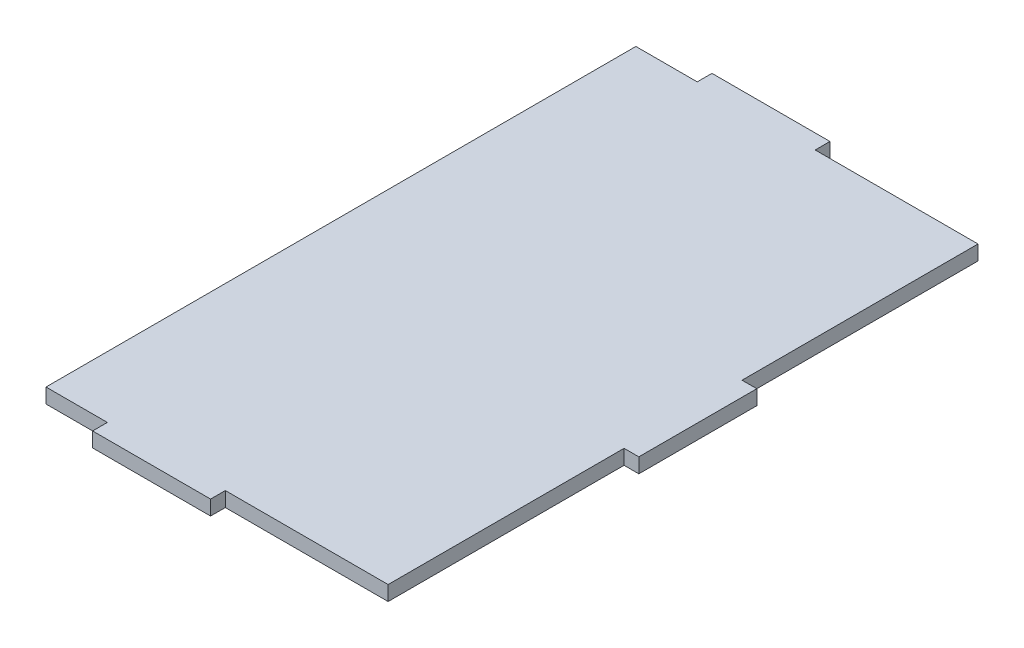
SolidWorks part; units mm, degrees
ref_plane "Front Plane" through (0, 0, 0) normal (0, 0, 1) x (1, 0, 0)
ref_plane "Top Plane" through (0, 0, 0) normal (0, 1, 0) x (1, 0, 0)
ref_plane "Right Plane" through (0, 0, 0) normal (1, 0, 0) x (0, 0, -1)
sketch "Sketch1" plane through (0, 0, 0) normal (0, 1, 0) x (1, 0, 0)
  line L1 (1.4817, 68.2625) -> (75.1417, 68.2625)
  line L2 (1.4817, 68.2625) -> (1.4817, -58.7375)
  line L3 (1.4817, -58.7375) -> (75.1417, -58.7375)
  line L4 (75.1417, 68.2625) -> (75.1417, -58.7375)
  dimension "D1" = 127
  dimension "D2" = 73.66
extrude "Boss-Extrude1" add sketch "Sketch1" along normal blind 3.175
sketch "Sketch2" plane through (75.1417, 0, 0) normal (1, 0, 0) x (0, 0, -1)
  line L0 (-58.7375, 3.175) -> (68.2625, 3.175) construction
  line L1 (-7.9375, 3.175) -> (17.4625, 3.175)
  line L2 (-7.9375, 3.175) -> (-7.9375, 0)
  line L3 (-7.9375, 0) -> (17.4625, 0)
  line L4 (17.4625, 3.175) -> (17.4625, 0)
  line L5 (-58.7375, 0) -> (68.2625, 0) construction
  line L6 (-58.7375, 3.175) -> (-58.7375, 0) construction
  point P10 (-58.7375, 1.5875)
  dimension "D1" = 25.4
  dimension "D2" = 50.8
extrude "Boss-Extrude2" add sketch "Sketch2" along normal blind 3.175
sketch "Sketch3" plane through (0, 0, 58.7375) normal (0, 0, 1) x (1, 0, 0)
  line L0 (1.4817, 3.175) -> (75.1417, 3.175) construction
  line L1 (14.6897, 3.175) -> (40.0897, 3.175)
  line L2 (14.6897, 3.175) -> (14.6897, 0)
  line L3 (14.6897, 0) -> (40.0897, 0)
  line L4 (40.0897, 3.175) -> (40.0897, 0)
  line L5 (1.4817, 0) -> (75.1417, 0) construction
  line L6 (75.1417, 3.175) -> (75.1417, 0) construction
  dimension "D1" = 25.4
  dimension "D2" = 35.052
extrude "Boss-Extrude3" add sketch "Sketch3" along normal blind 3.175 contours L2 L3 L4 L1
sketch "Sketch5" plane through (0, 0, -68.2625) normal (0, 0, -1) x (-1, 0, 0)
  line L1 (-40.0897, 3.175) -> (-14.6897, 3.175)
  line L2 (-40.0897, 3.175) -> (-40.0897, 0)
  line L3 (-40.0897, 0) -> (-14.6897, 0)
  line L4 (-14.6897, 3.175) -> (-14.6897, 0)
extrude "Boss-Extrude4" add sketch "Sketch5" along normal blind 3.175
